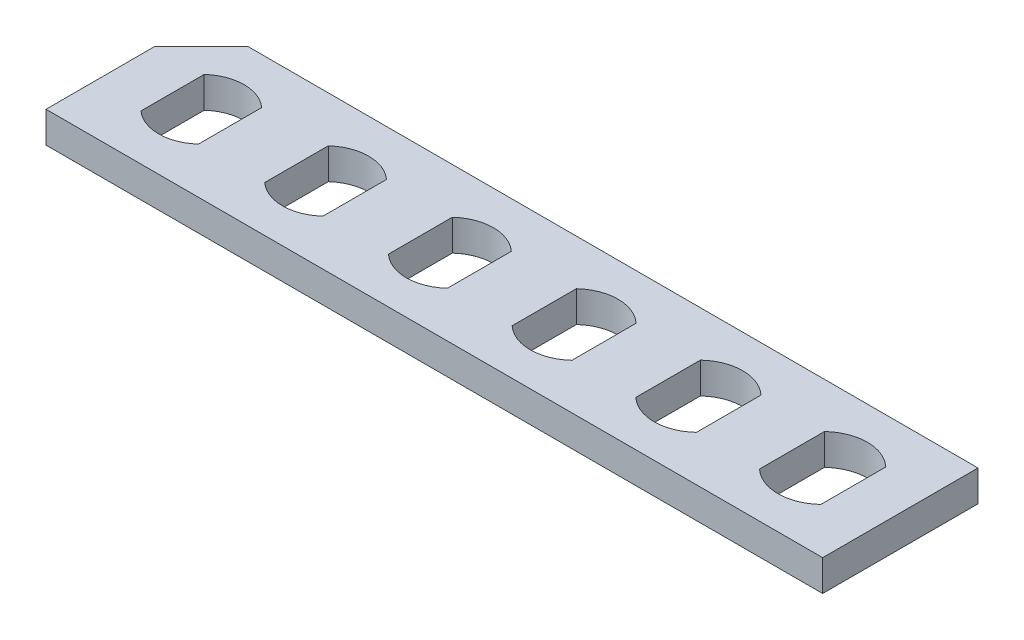
SolidWorks part; units mm, degrees
ref_plane "Front Plane" through (0, 0, 0) normal (0, 0, 1) x (1, 0, 0)
ref_plane "Top Plane" through (0, 0, 0) normal (0, 1, 0) x (1, 0, 0)
ref_plane "Right Plane" through (0, 0, 0) normal (1, 0, 0) x (0, 0, -1)
sketch "Sketch1" plane through (0, 0, 0) normal (0, 1, 0) x (1, 0, 0)
  line L1 (0, 0) -> (50, 0)
  line L2 (0, 0) -> (0, 10)
  line L3 (0, 10) -> (50, 10)
  line L4 (50, 0) -> (50, 10)
  line L5 (0, 5) -> (50, 5) construction
  line L6 (3.15, 7.0347) -> (3.15, 2.9653)
  line L7 (6.85, 2.9653) -> (6.85, 7.0347)
  line L8 (11.125, 7.0457) -> (11.125, 2.9543)
  line L9 (14.875, 2.9543) -> (14.875, 7.0457)
  line L10 (19.1, 7.0567) -> (19.1, 2.9433)
  line L11 (22.9, 2.9433) -> (22.9, 7.0567)
  line L12 (27.075, 7.0676) -> (27.075, 2.9324)
  line L13 (30.925, 2.9324) -> (30.925, 7.0676)
  line L16 (38.95, 2.9215) -> (38.95, 7.0785)
  line L17 (35.05, 7.0785) -> (35.05, 2.9215)
  line L21 (46.975, 2.9107) -> (46.975, 7.0893)
  line L22 (43.025, 7.0893) -> (43.025, 2.9107)
  arc A0 (3.15, 2.9653) -> (6.85, 2.9653) centre (5, 5) ccw
  arc A1 (6.85, 7.0347) -> (3.15, 7.0347) centre (5, 5) ccw
  arc A2 (11.125, 2.9543) -> (14.875, 2.9543) centre (13, 5) ccw
  arc A3 (14.875, 7.0457) -> (11.125, 7.0457) centre (13, 5) ccw
  arc A4 (19.1, 2.9433) -> (22.9, 2.9433) centre (21, 5) ccw
  arc A5 (22.9, 7.0567) -> (19.1, 7.0567) centre (21, 5) ccw
  arc A6 (27.075, 2.9324) -> (30.925, 2.9324) centre (29, 5) ccw
  arc A7 (30.925, 7.0676) -> (27.075, 7.0676) centre (29, 5) ccw
  arc A8 (38.95, 7.0785) -> (35.05, 7.0785) centre (37, 5) ccw
  arc A9 (35.05, 2.9215) -> (38.95, 2.9215) centre (37, 5) ccw
  arc A10 (43.025, 2.9107) -> (46.975, 2.9107) centre (45, 5) ccw
  arc A11 (46.975, 7.0893) -> (43.025, 7.0893) centre (45, 5) ccw
  dimension "D3" = 5.5
  dimension "D7" = 5.55
  dimension "D9" = 5.6
  dimension "D11" = 5.65
  dimension "D16" = 5.7
  dimension "D19" = 5.75
  dimension "D1" = 10
  dimension "D4" = 3.7
  dimension "D5" = 5
  dimension "D6" = 5
  dimension "D8" = 3.75
  dimension "D10" = 3.8
  dimension "D12" = 3.85
  dimension "D13" = 8
  dimension "D14" = 8
  dimension "D15" = 8
  dimension "D17" = 3.9
  dimension "D18" = 8
  dimension "D20" = 3.95
  dimension "D21" = 8
  dimension "D22" = 5
extrude "Boss-Extrude1" add sketch "Sketch1" along normal blind 2
sketch "Sketch2" plane through (0, 2, 0) normal (0, 1, 0) x (1, 0, 0)
  line L0 (0, 7) -> (3, 10)
  line L1 (0, 10) -> (0, 0) construction
  line L2 (50, 10) -> (0, 10) construction
  line L3 (0, 7) -> (0, 10)
  line L4 (0, 10) -> (3, 10)
  dimension "D1" = 3
extrude "Cut-Extrude1" cut sketch "Sketch2" against normal through all
equation "\"D1@Sketch1\"=\"D5@Sketch1\"*2"
